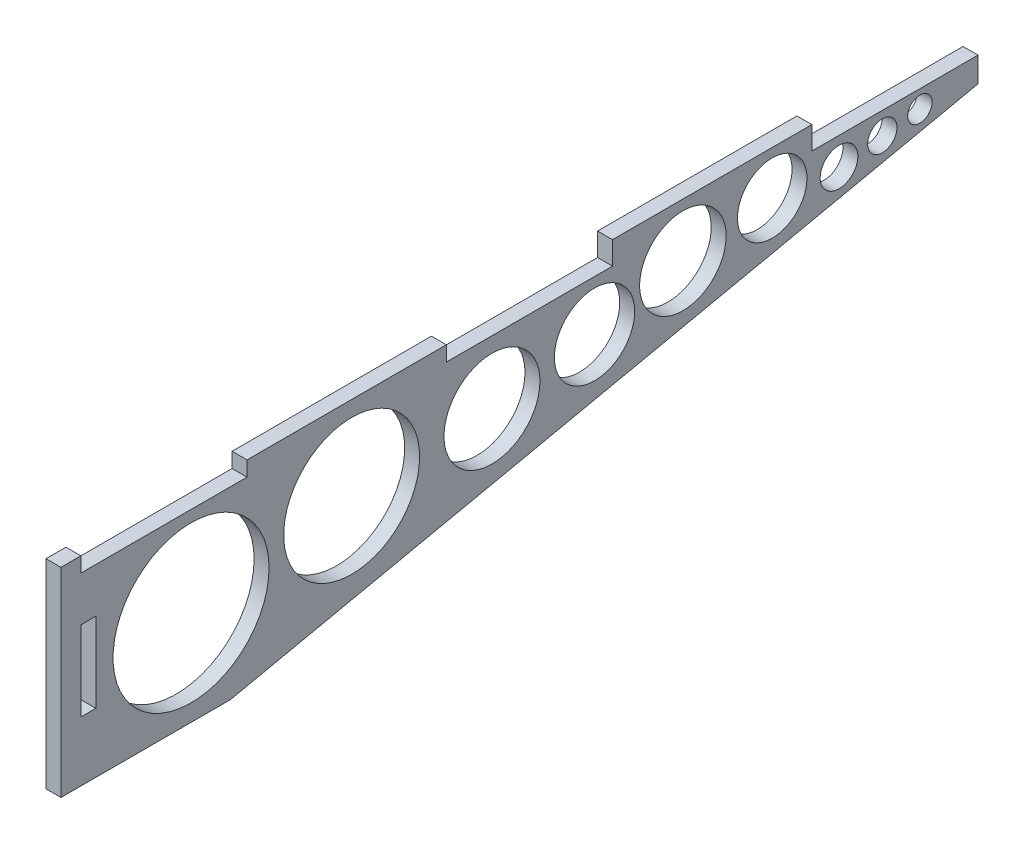
SolidWorks part; units mm, degrees
ref_plane "Front Plane" through (0, 0, 0) normal (0, 0, 1) x (1, 0, 0)
ref_plane "Top Plane" through (0, 0, 0) normal (0, 1, 0) x (1, 0, 0)
ref_plane "Right Plane" through (0, 0, 0) normal (1, 0, 0) x (0, 0, -1)
sketch "Sketch1" plane through (0, 0, 0) normal (1, 0, 0) x (0, 0, -1)
  line L0 (180, -8) -> (30, -40)
  line L1 (0, 0) -> (180, 0)
  line L2 (0, 0) -> (0, -40) construction
  line L3 (0, -40) -> (30, -40)
  line L4 (180, 0) -> (180, -8)
  line L5 (30, -40) -> (180, -40) construction
  line L6 (180, -8) -> (180, -40) construction
  line L7 (0, -20) -> (180, -20) construction
  line L8 (0, 0) -> (33.3333, 0)
  line L9 (0, 0) -> (0, -3)
  line L10 (0, -3) -> (33.3333, -3)
  line L11 (33.3333, 0) -> (33.3333, -3)
  line L12 (73.3333, 0) -> (106.6667, 0)
  line L13 (73.3333, 0) -> (73.3333, -3)
  line L14 (73.3333, -3) -> (106.6667, -3)
  line L15 (106.6667, 0) -> (106.6667, -3)
  line L16 (146.6667, 0) -> (180, 0)
  line L17 (146.6667, 0) -> (146.6667, -3)
  line L18 (146.6667, -3) -> (180, -3)
  line L19 (180, 0) -> (180, -3)
  line L20 (0, -12) -> (3, -12)
  line L21 (0, -12) -> (0, -28)
  line L22 (0, -28) -> (3, -28)
  line L23 (3, -12) -> (3, -28)
  line L24 (0, -40) -> (-4, -40)
  line L25 (-4, -40) -> (-4, 0)
  line L26 (-4, 0) -> (0, 0)
  dimension "D1" = 40
  dimension "D2" = 180
  dimension "D3" = 8
  dimension "D4" = 30
  dimension "D5" = 3
  dimension "D6" = 40
  dimension "D7" = 40
  dimension "D8" = 4
  dimension "D10" = 9
  dimension "D11" = 16
extrude "Boss-Extrude1" add sketch "Sketch1" along normal blind 3
sketch "Sketch2" plane through (3, 0, 0) normal (1, 0, 0) x (0, 0, -1)
  line L0 (146.6667, 0) -> (146.6667, -3) construction
  line L1 (106.6667, 0) -> (146.6667, 0)
  line L2 (106.6667, 0) -> (106.6667, 1.6)
  line L3 (106.6667, 1.6) -> (146.6667, 1.6)
  line L4 (146.6667, 0) -> (146.6667, 1.6)
  dimension "D1" = 1.6
extrude "Boss-Extrude2" add sketch "Sketch2" against normal blind 3
sketch "Sketch3" plane through (3, 0, 0) normal (1, 0, 0) x (0, 0, -1)
  circle A0 centre (22.1046, -20.9561) radius 15.6511
  circle A1 centre (54.3289, -16.7523) radius 13.6364
  circle A2 centre (82.4831, -15.6732) radius 9.6254
  circle A3 centre (103.0578, -13.0601) radius 8.0557
  circle A4 centre (120.792, -9.1283) radius 8.6793
  circle A5 centre (138.7079, -7.1923) radius 6.974
  circle A6 centre (168.3401, -6.5485) radius 2.4464
  circle A7 centre (152.1174, -8.5023) radius 3.7795
  circle A9 centre (160.8012, -7.4207) radius 2.9435
extrude "Cut-Extrude1" cut sketch "Sketch3" against normal blind 10
